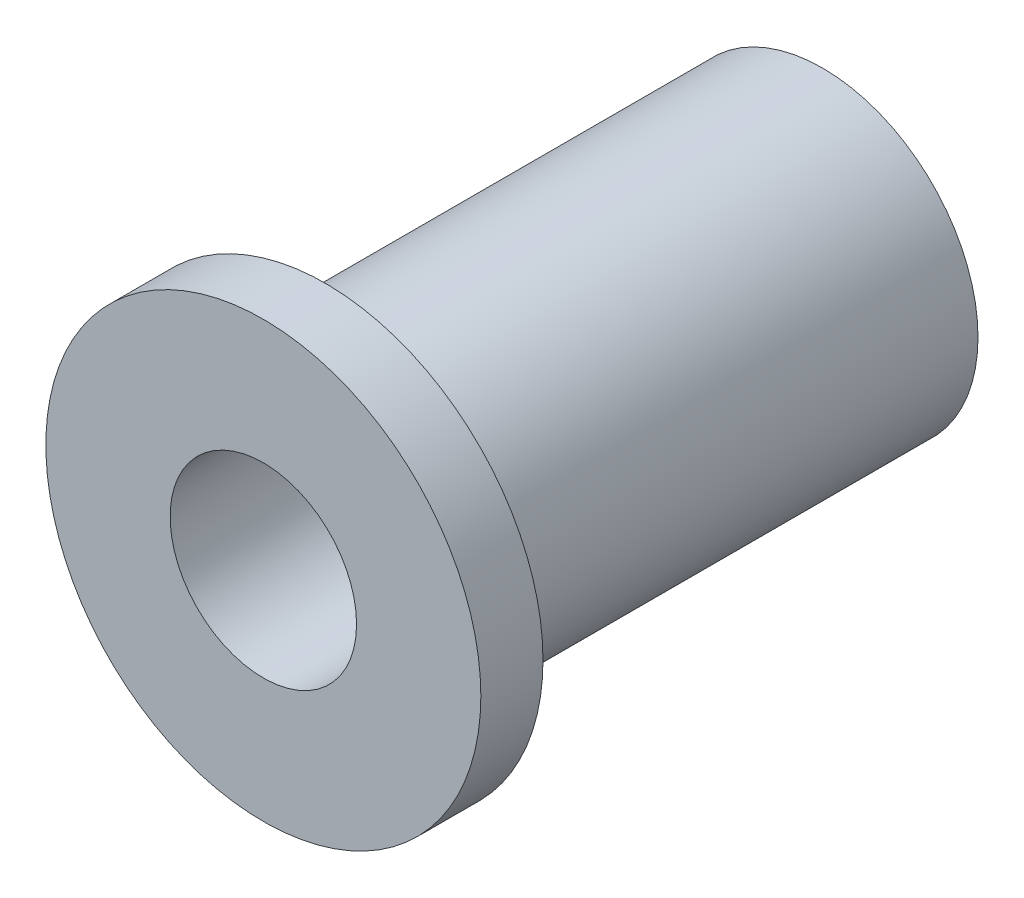
SolidWorks part; units mm, degrees
material "Commercial Bronze, UNS C22000 (90-10 Bronze)"
ref_plane "Front Plane" through (0, 0, 0) normal (0, 0, 1) x (1, 0, 0)
ref_plane "Top Plane" through (0, 0, 0) normal (0, 1, 0) x (1, 0, 0)
ref_plane "Right Plane" through (0, 0, 0) normal (1, 0, 0) x (0, 0, -1)
sketch "Sketch1" plane through (0, 0, 0) normal (0, 0, 1) x (1, 0, 0)
  circle A0 centre (0, 0) radius 5.5562
  dimension "D1" = 11.1125
extrude "Boss-Extrude1" add sketch "Sketch1" along normal blind 1.5875
sketch "Sketch2" plane through (0, 0, 0) normal (0, 0, -1) x (-1, 0, 0)
  circle A0 centre (0, 0) radius 3.9688
  dimension "D1" = 7.9375
extrude "Boss-Extrude2" add sketch "Sketch2" along normal blind 12.7
sketch "Sketch3" plane through (0, 0, 1.5875) normal (0, 0, 1) x (1, 0, 0)
  circle A0 centre (0, 0) radius 2.3813
  dimension "D1" = 4.7625
extrude "Cut-Extrude1" cut sketch "Sketch3" against normal through all
